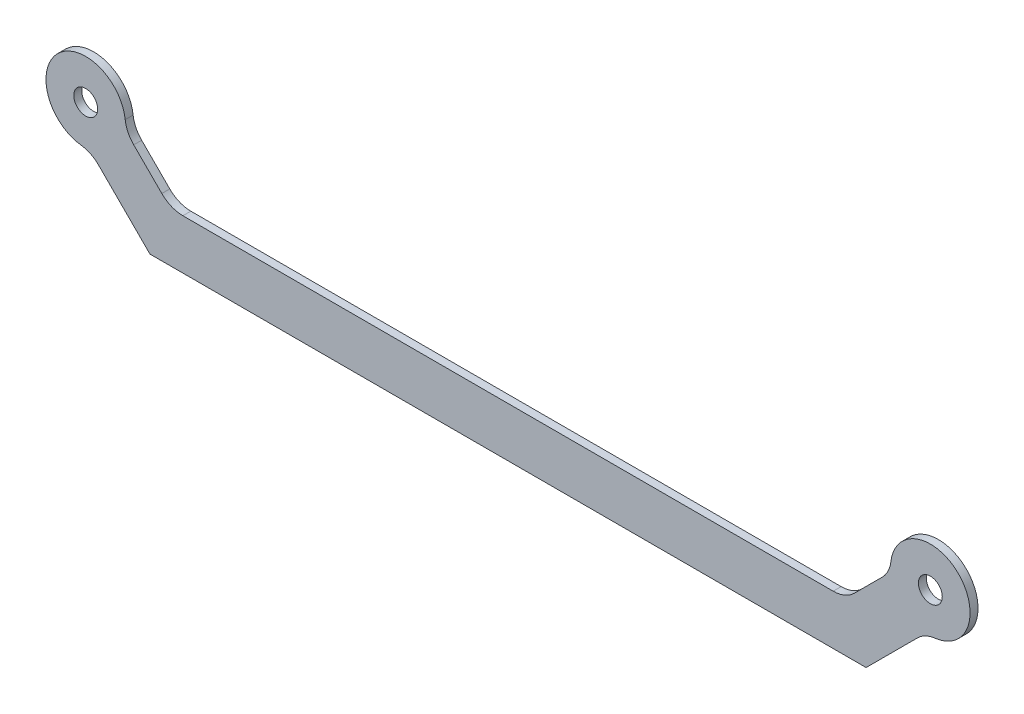
SolidWorks part; units mm, degrees
material "Hexcel AS4C (3000 Filaments)"
ref_plane "Front Plane" through (0, 0, 0) normal (0, 0, 1) x (1, 0, 0)
ref_plane "Top Plane" through (0, 0, 0) normal (0, 1, 0) x (1, 0, 0)
ref_plane "Right Plane" through (0, 0, 0) normal (1, 0, 0) x (0, 0, -1)
sketch "Sketch3" plane through (0, 0, 0) normal (0, 0, 1) x (1, 0, 0)
  line L0 (0, 0) -> (0, -24.7028) construction
  line L1 (-42.5, 0) -> (-35, -7.5) construction
  line L2 (-35, -7.5) -> (35, -7.5) construction
  line L3 (42.5, 0) -> (35, -7.5) construction
  line L4 (-42.5, 0) -> (42.5, 0) construction
  line L5 (-40.7322, 1.7678) -> (-33.9645, -5)
  line L6 (-33.9645, -5) -> (33.9645, -5)
  line L7 (40.7322, 1.7678) -> (33.9645, -5)
  line L8 (-44.2678, -1.7678) -> (-36.0355, -10)
  line L9 (-36.0355, -10) -> (36.0355, -10)
  line L10 (44.2678, -1.7678) -> (36.0355, -10)
  arc A0 (-40.7322, 1.7678) -> (-44.2678, -1.7678) centre (-42.5, 0) ccw
  arc A1 (40.7322, 1.7678) -> (44.2678, -1.7678) centre (42.5, 0) cw
  point P11 (0, -7.5)
  dimension "D1" = 85
  dimension "D4" = 2.5
  dimension "D2" = 135
  dimension "D3" = 70
extrude "Boss-Extrude1" add sketch "Sketch3" along normal blind 0.8
sketch "Sketch7" plane through (0, 0, 0.8) normal (0, 0, 1) x (1, 0, 0)
  circle A0 centre (-42.5, 0) radius 4
  circle A1 centre (42.5, 0) radius 4
  dimension "D1" = 8
extrude "Boss-Extrude2" add sketch "Sketch7" against normal up to surface (0.8 mm away) up to face at (0, -3.3081, 0)
fillet "Fillet1" radius 3 6 edges at (33.9645, -5, 0.4) (-33.9645, -5, 0.4) (38.5243, -0.4402, 0.4) (42.0598, -3.9757, 0.4) (-42.0598, -3.9757, 0.4) (-38.5243, -0.4402, 0.4)
hole_wizard "M2 Clearance Hole1" positions "Sketch9" profile "Sketch8" hole size "M2" standard "DIN"
sketch "Sketch9" plane through (0, 0, 0.8) normal (0, 0, 1) x (1, 0, 0)
  point P0 (-42.5, 0)
  point P1 (42.5, 0)
sketch "Sketch8" plane through (-42.5, 0, 0.8) normal (1, 0, 0) x (0, -1, 0)
  line L0 (0, 0) -> (0, 30.5)
  line L1 (0, 30.5) -> (1.2, 30.5)
  line L2 (1.2, 30.5) -> (1.2, 0)
  line L5 (1.2, 0) -> (0, 0)
  line L10 (0, 30.5) -> (-1.2, 30.5) construction
  line L11 (0, -6.35) -> (0, 107.95) construction
  dimension "Hole Dia." = 2.4
  dimension "Hole Depth" = 30.5
  dimension "Drill Angle" = 180
